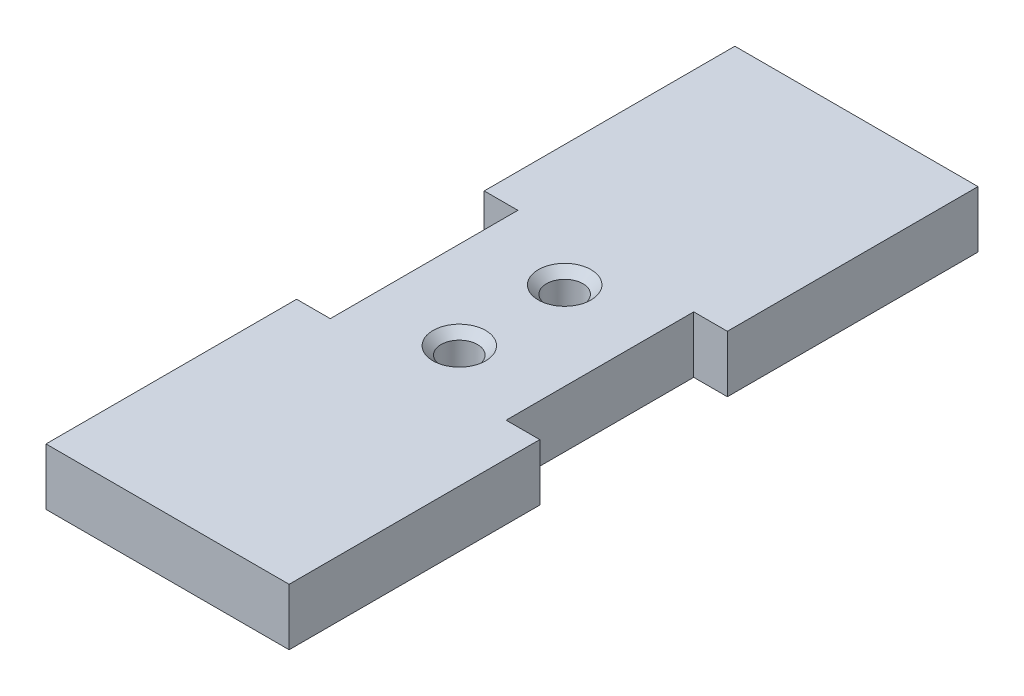
SolidWorks part; units mm, degrees
ref_plane "Front Plane" through (0, 0, 0) normal (0, 0, 1) x (1, 0, 0)
ref_plane "Top Plane" through (0, 0, 0) normal (0, 1, 0) x (1, 0, 0)
ref_plane "Right Plane" through (0, 0, 0) normal (1, 0, 0) x (0, 0, -1)
sketch "Sketch1" plane through (0, 0, 0) normal (0, 1, 0) x (1, 0, 0)
  line L1 (0, 0) -> (30, 0)
  line L2 (0, 0) -> (0, 85)
  line L3 (0, 85) -> (30, 85)
  line L4 (30, 0) -> (30, 85)
  line L5 (0, 0) -> (30, 85) construction
  line L6 (0, 85) -> (30, 0) construction
  point P4 (15, 42.5)
  dimension "D1" = 30
  dimension "D2" = 85
extrude "Boss-Extrude1" add sketch "Sketch1" along normal blind 7
sketch "Sketch2" plane through (0, 7, 0) normal (0, 1, 0) x (1, 0, 0)
  line L0 (0, 42.5) -> (30, 42.5) construction
  line L1 (0, 85) -> (0, 0) construction
  line L2 (30, 0) -> (30, 85) construction
  line L3 (30, 54.075) -> (30, 30.925) construction
  line L4 (0, 54.075) -> (4.15, 54.075)
  line L5 (4.15, 54.075) -> (4.15, 30.925)
  line L6 (4.15, 30.925) -> (0, 30.925)
  line L7 (30, 54.075) -> (25.85, 54.075)
  line L8 (25.85, 54.075) -> (25.85, 30.925)
  line L9 (25.85, 30.925) -> (30, 30.925)
  line L10 (15, 42.5) -> (15, 45.6407) construction
  line L11 (15, 45.6407) -> (4.15, 45.6407) construction
  line L12 (15, 45.6407) -> (25.85, 45.6407) construction
  line L13 (0, 54.075) -> (0, 30.925)
  line L14 (30, 54.075) -> (30, 30.925)
  point P8 (30, 42.5)
  dimension "D1" = 23.15
  dimension "D2" = 21.7
extrude "Cut-Extrude1" cut sketch "Sketch2" against normal through all
sketch "Sketch3" plane through (0, 7, 0) normal (0, 1, 0) x (1, 0, 0)
  line L0 (15, 42.5) -> (15, 54) construction
  line L3 (4.15, 42.5) -> (25.85, 42.5) construction
  line L4 (4.15, 30.925) -> (4.15, 54.075) construction
  line L5 (25.85, 54.075) -> (25.85, 30.925) construction
  circle A0 centre (15, 49) radius 2.25
  circle A1 centre (15, 36) radius 2.25
  point P15 (17.8362, 44.9233)
  point P16 (0, 0)
  point P17 (15, 45.2646)
  dimension "D1" = 4.5
  dimension "D2" = 11.5
  dimension "D3" = 5
extrude "Cut-Extrude2" cut sketch "Sketch3" against normal through all
chamfer "Chamfer1" distance 1 angle 45 2 edges at (15, 7, -38.25) (15, 7, -46.75)
